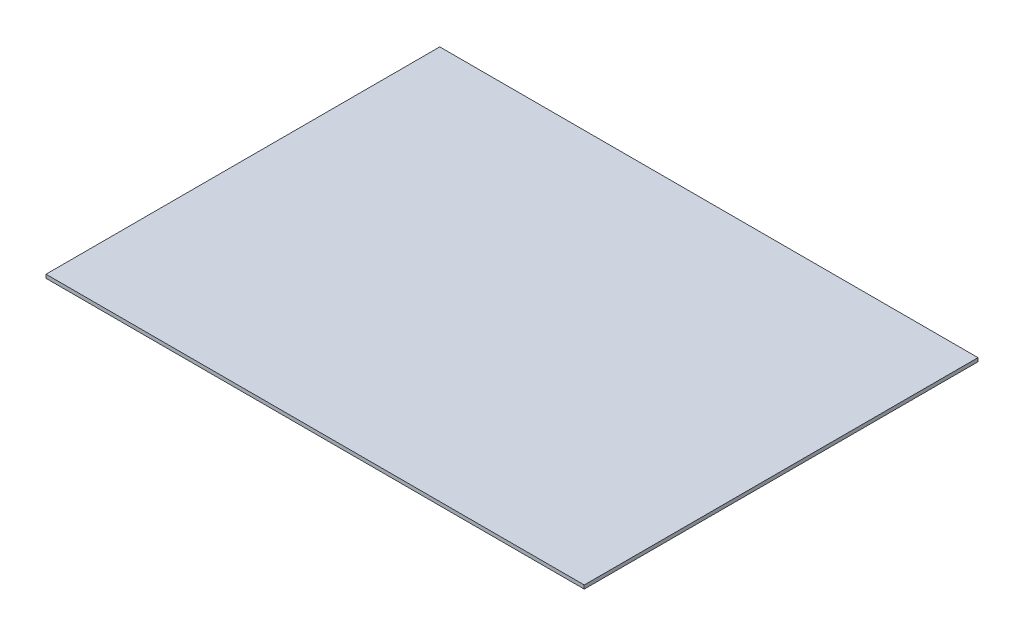
SolidWorks part; units mm, degrees
ref_plane "Front Plane" through (0, 0, 0) normal (0, 0, 1) x (1, 0, 0)
ref_plane "Top Plane" through (0, 0, 0) normal (0, 1, 0) x (1, 0, 0)
ref_plane "Right Plane" through (0, 0, 0) normal (1, 0, 0) x (0, 0, -1)
sketch "Sketch1" plane through (0, 0, 0) normal (1, 0, 0) x (0, 0, -1)
  line L0 (-26.6783, 0) -> (191.3217, 0)
  line L1 (119.9, 0) -> (-119.9, 0) construction
  line L2 (-26.6783, 0) -> (-26.6783, 2)
  line L3 (191.3217, 0) -> (191.3217, 2)
  line L4 (191.3217, 2) -> (-26.6783, 2)
  dimension "D1" = 218
  dimension "D2" = 2
extrude "Boss-Extrude1" add sketch "Sketch1" along normal blind 298 contours L4 L2 L0 L3
